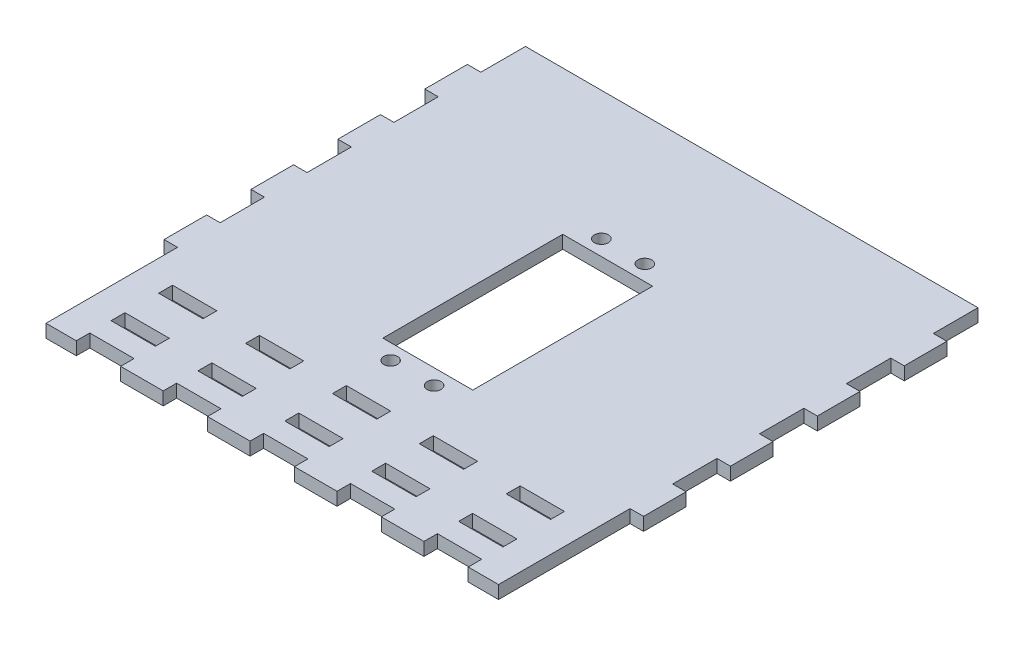
SolidWorks part; units mm, degrees
ref_plane "Front Plane" through (0, 0, 0) normal (0, 0, 1) x (1, 0, 0)
ref_plane "Top Plane" through (0, 0, 0) normal (0, 1, 0) x (1, 0, 0)
ref_plane "Right Plane" through (0, 0, 0) normal (1, 0, 0) x (0, 0, -1)
sketch "Sketch1" plane through (0, 0, 0) normal (0, 1, 0) x (1, 0, 0)
  line L0 (0, 0) -> (0, 21.0585) construction
  line L1 (10.05, -30.75) -> (-10.05, -30.75) construction
  line L2 (-10.05, -30.75) -> (-10.05, 10.05) construction
  line L3 (10.05, 10.05) -> (-10.05, 10.05) construction
  line L4 (10.05, -30.75) -> (10.05, 10.05) construction
  line L5 (10.05, -30.75) -> (-10.05, -30.75) construction
  line L6 (-10.05, -30.75) -> (-10.05, 10.05) construction
  line L7 (10.05, 10.05) -> (-10.05, 10.05) construction
  line L8 (10.05, -30.75) -> (10.05, 10.05) construction
  line L9 (-10.35, -31.05) -> (-10.35, 10.35)
  line L10 (10.35, 10.35) -> (-10.35, 10.35)
  line L11 (10.35, -31.05) -> (10.35, 10.35)
  line L12 (10.35, -31.05) -> (-10.35, -31.05)
  line L13 (-36.8722, 43.5014) -> (-36.8722, -66.843) construction
  line L14 (-55.1722, 43.5014) -> (55.1722, 43.5014)
  line L15 (-55.1722, 43.5014) -> (-55.1722, -66.843)
  line L16 (-55.1722, -66.843) -> (55.1722, -66.843)
  line L17 (55.1722, 43.5014) -> (55.1722, -66.843)
  line L18 (36.8722, 43.5014) -> (36.8722, -66.843) construction
  line L19 (0, 43.5014) -> (0, -66.843) construction
  line L20 (-36.8722, 39.9014) -> (-36.8722, -63.843) construction
  line L21 (0, -11.6708) -> (55.1722, -11.6708) construction
  line L22 (0, -11.6708) -> (55.1722, -66.843) construction
  line L23 (-52.1722, 40.5014) -> (-52.1722, -63.843) construction
  line L24 (52.1722, 40.5014) -> (52.1722, -63.843) construction
  line L25 (-52.1722, 40.5014) -> (52.1722, 40.5014) construction
  line L26 (-52.1722, -63.843) -> (52.1722, -63.843) construction
  line L27 (-52.1722, -63.843) -> (-55.1722, -63.843) construction
  line L28 (-52.1722, -63.843) -> (-52.1722, -66.843) construction
  line L29 (52.1722, 40.5014) -> (52.1722, 43.5014) construction
  line L30 (52.1722, 40.5014) -> (55.1722, 40.5014) construction
  line L31 (-52.1722, -11.6708) -> (-55.1722, -11.6708) construction
  line L32 (56.7, -129.793) -> (59.7, -129.793) construction
  line L33 (-55.1722, -48.543) -> (55.1722, -48.543) construction
  line L34 (-55.1722, -47.793) -> (55.1722, -47.793) construction
  line L35 (55.1722, -47.793) -> (-55.1722, -47.793) construction
  line L36 (55.1722, -44.793) -> (-55.1722, -44.793) construction
  line L37 (-49.1722, -47.793) -> (-49.1722, -44.793) construction
  line L38 (-49.1722, -46.293) -> (-52.1722, -46.293) construction
  line L39 (-55.1722, -58.743) -> (55.1722, -58.743) construction
  line L40 (55.1722, -58.743) -> (-55.1722, -58.743) construction
  line L41 (-55.1722, -55.743) -> (55.1722, -55.743) construction
  line L42 (-49.1722, -55.743) -> (-49.1722, -58.743) construction
  circle A0 centre (0, 0) radius 21.0585 construction
  arc A1 (21.0585, 3.843) -> (-21.0585, 3.843) centre (0, 3.843) ccw construction
  circle A2 centre (-5, -34.6) radius 2 construction
  circle A3 centre (5, -34.6) radius 2 construction
  circle A4 centre (5, 13.9) radius 2 construction
  circle A5 centre (-5, 13.9) radius 2 construction
  circle A6 centre (-5, -34.6) radius 2 construction
  circle A7 centre (5, -34.6) radius 2 construction
  circle A8 centre (5, 13.9) radius 2 construction
  circle A9 centre (-5, 13.9) radius 2 construction
  circle A10 centre (-5, 13.9) radius 1.6
  circle A11 centre (5, 13.9) radius 1.6
  circle A12 centre (5, -34.6) radius 1.6
  circle A13 centre (-5, -34.6) radius 1.6
  dimension "D2" = 3.2
  dimension "D1" = 0.3
extrude "Boss-Extrude1" add sketch "Sketch1" along normal up to vertex (3 mm away)
sketch "Sketch2" plane through (0, 0, 0) normal (0, 1, 0) x (1, 0, 0)
  line L0 (0, -11.6708) -> (55.1722, -11.6708) construction
  line L1 (0, -11.6708) -> (0, 43.5014) construction
  line L2 (0, -11.6708) -> (55.1722, 43.5014) construction
  line L3 (5, 43.5014) -> (5, 40.5014)
  line L4 (15, 40.5014) -> (15, 43.5014)
  line L5 (25, 40.5014) -> (25, 43.5014)
  line L6 (35, 40.5014) -> (35, 43.5014)
  line L7 (45, 40.5014) -> (45, 43.5014)
  line L8 (-55.1722, 43.5014) -> (55.1722, 43.5014) construction
  line L9 (-52.1722, 40.5014) -> (52.1722, 40.5014) construction
  line L10 (52.1722, 33.3292) -> (55.1722, 33.3292)
  line L11 (52.1722, 23.3292) -> (55.1722, 23.3292)
  line L12 (52.1722, 13.3292) -> (55.1722, 13.3292)
  line L13 (52.1722, 3.3292) -> (55.1722, 3.3292)
  line L14 (55.1722, -6.6708) -> (52.1722, -6.6708)
  line L15 (55.1722, -16.6708) -> (52.1722, -16.6708)
  line L16 (52.1722, -26.6708) -> (55.1722, -26.6708)
  line L17 (52.1722, -36.6708) -> (55.1722, -36.6708)
  line L18 (52.1722, -46.6708) -> (55.1722, -46.6708)
  line L19 (52.1722, -56.6708) -> (55.1722, -56.6708)
  line L20 (45, -63.843) -> (45, -66.843)
  line L21 (35, -63.843) -> (35, -66.843)
  line L22 (25, -63.843) -> (25, -66.843)
  line L23 (15, -63.843) -> (15, -66.843)
  line L24 (5, -66.843) -> (5, -63.843)
  line L25 (-5, -66.843) -> (-5, -63.843)
  line L26 (-15, -63.843) -> (-15, -66.843)
  line L27 (-25, -63.843) -> (-25, -66.843)
  line L28 (-35, -63.843) -> (-35, -66.843)
  line L29 (-45, -63.843) -> (-45, -66.843)
  line L30 (-52.1722, -56.6708) -> (-55.1722, -56.6708)
  line L31 (-52.1722, -46.6708) -> (-55.1722, -46.6708)
  line L32 (-52.1722, -36.6708) -> (-55.1722, -36.6708)
  line L33 (-52.1722, -26.6708) -> (-55.1722, -26.6708)
  line L34 (-55.1722, -16.6708) -> (-52.1722, -16.6708)
  line L35 (-55.1722, -6.6708) -> (-52.1722, -6.6708)
  line L36 (-52.1722, 3.3292) -> (-55.1722, 3.3292)
  line L37 (-52.1722, 13.3292) -> (-55.1722, 13.3292)
  line L38 (-52.1722, 23.3292) -> (-55.1722, 23.3292)
  line L39 (-52.1722, 33.3292) -> (-55.1722, 33.3292)
  line L40 (-45, 40.5014) -> (-45, 43.5014)
  line L41 (-35, 40.5014) -> (-35, 43.5014)
  line L42 (-25, 40.5014) -> (-25, 43.5014)
  line L43 (-15, 40.5014) -> (-15, 43.5014)
  line L44 (-5, 43.5014) -> (-5, 40.5014)
  line L45 (55.1722, -44.793) -> (-55.1722, -44.793) construction
  line L48 (-55.1722, -47.793) -> (55.1722, -47.793) construction
  line L49 (55.1722, -44.793) -> (-55.1722, -44.793)
  line L50 (-55.1722, -47.793) -> (55.1722, -47.793)
  line L51 (-15, -47.793) -> (-15, -44.793)
  line L52 (-5, -47.793) -> (-5, -44.793)
  line L53 (5, -47.793) -> (5, -44.793)
  line L54 (15, -47.793) -> (15, -44.793)
  line L55 (25, -47.793) -> (25, -44.793)
  line L56 (35, -47.793) -> (35, -44.793)
  line L57 (45, -47.793) -> (45, -44.793)
  line L58 (-25, -47.793) -> (-25, -44.793)
  line L59 (-35, -47.793) -> (-35, -44.793)
  line L60 (-45, -47.793) -> (-45, -44.793)
  line L61 (52.1722, -63.843) -> (52.1722, -66.843)
  line L62 (52.1722, 40.5014) -> (52.1722, -63.843) construction
  line L63 (55.1722, -63.843) -> (-55.1722, -63.843) construction
  line L64 (-55.1722, -66.843) -> (55.1722, -66.843) construction
  line L65 (-55.1722, -55.743) -> (55.1722, -55.743) construction
  line L66 (-55.1722, -58.743) -> (55.1722, -58.743) construction
  line L67 (-55.1722, -55.743) -> (55.1722, -55.743)
  line L68 (-55.1722, -58.743) -> (55.1722, -58.743)
  line L69 (-45, -55.743) -> (-45, -58.743)
  line L70 (-15, -55.743) -> (-15, -58.743)
  line L71 (-35, -55.743) -> (-35, -58.743)
  line L72 (-25, -55.743) -> (-25, -58.743)
  line L73 (-5, -58.743) -> (-5, -55.743)
  line L74 (5, -58.743) -> (5, -55.743)
  line L75 (15, -58.743) -> (15, -55.743)
  line L76 (25, -58.743) -> (25, -55.743)
  line L77 (45, -55.743) -> (45, -58.743)
  line L78 (35, -58.743) -> (35, -55.743)
sketch "Sketch3" plane through (0, 0, 0) normal (0, 1, 0) x (1, 0, 0)
  line L0 (0, -11.6708) -> (55.1722, 43.5014) construction
  line L1 (0, -11.6708) -> (55.1722, -11.6708) construction
  line L2 (0, -11.6708) -> (0, 43.5014) construction
  line L3 (52.1722, -6.6708) -> (52.0722, -6.6708) construction
  line L4 (52.0722, 3.4292) -> (55.2722, 3.4292)
  line L5 (52.0722, 3.4292) -> (52.0722, -6.7708)
  line L6 (52.0722, -6.7708) -> (55.2722, -6.7708)
  line L7 (55.2722, 3.4292) -> (55.2722, -6.7708)
  line L8 (52.0722, 13.2292) -> (55.2722, 13.2292)
  line L9 (52.0722, 13.2292) -> (52.0722, 23.4292)
  line L10 (52.0722, 23.4292) -> (55.2722, 23.4292)
  line L11 (55.2722, 13.2292) -> (55.2722, 23.4292)
  line L12 (52.0722, 33.2292) -> (55.2722, 33.2292)
  line L13 (52.0722, 33.2292) -> (52.0722, 43.6014)
  line L14 (52.0722, 43.6014) -> (55.2722, 43.6014)
  line L15 (55.2722, 33.2292) -> (55.2722, 43.6014)
  line L16 (52.1722, -6.6708) -> (52.1722, -6.7708) construction
  line L17 (55.1722, 3.3292) -> (55.2722, 3.3292) construction
  line L18 (55.1722, 3.3292) -> (55.1722, 3.4292) construction
  line L19 (52.1722, 13.3292) -> (52.1722, 13.2292) construction
  line L20 (52.1722, 23.3292) -> (52.1722, 23.4292) construction
  line L21 (52.1722, 33.3292) -> (52.1722, 33.2292) construction
  line L22 (52.1722, 43.5014) -> (52.1722, 43.6014) construction
  line L23 (45, -44.793) -> (45, -44.693) construction
  line L24 (45.1, -47.893) -> (34.9, -47.893)
  line L25 (45.1, -47.893) -> (45.1, -44.693)
  line L26 (45.1, -44.693) -> (34.9, -44.693)
  line L27 (52.0722, -26.7708) -> (55.2722, -26.7708)
  line L28 (52.0722, -26.7708) -> (52.0722, -16.5708)
  line L29 (52.0722, -16.5708) -> (55.2722, -16.5708)
  line L30 (55.2722, -26.7708) -> (55.2722, -16.5708)
  line L31 (34.9, -47.893) -> (34.9, -44.693)
  line L32 (25.1, -47.893) -> (14.9, -47.893)
  line L33 (25.1, -47.893) -> (25.1, -44.693)
  line L34 (25.1, -44.693) -> (14.9, -44.693)
  line L35 (14.9, -47.893) -> (14.9, -44.693)
  line L36 (5.1, -47.893) -> (-5.1, -47.893)
  line L37 (5.1, -47.893) -> (5.1, -44.693)
  line L38 (5.1, -44.693) -> (-5.1, -44.693)
  line L39 (-5.1, -47.893) -> (-5.1, -44.693)
  line L40 (45, -47.793) -> (45, -47.893) construction
  line L41 (45, -44.793) -> (45.1, -44.793) construction
  line L42 (35, -44.793) -> (34.9, -44.793) construction
  line L43 (25, -44.793) -> (25.1, -44.793) construction
  line L44 (15, -44.793) -> (14.9, -44.793) construction
  line L45 (5, -44.793) -> (5.1, -44.793) construction
  line L46 (-25.1, -47.893) -> (-14.9, -47.893)
  line L47 (-14.9, -47.893) -> (-14.9, -44.693)
  line L48 (-25.1, -44.693) -> (-14.9, -44.693)
  line L49 (-25.1, -47.893) -> (-25.1, -44.693)
  line L50 (-45.1, -47.893) -> (-34.9, -47.893)
  line L51 (-45.1, -47.893) -> (-45.1, -44.693)
  line L52 (-45.1, -44.693) -> (-34.9, -44.693)
  line L53 (-34.9, -47.893) -> (-34.9, -44.693)
  line L54 (-52.0722, 33.2292) -> (-55.2722, 33.2292)
  line L55 (-55.2722, 33.2292) -> (-55.2722, 43.6014)
  line L56 (-52.0722, 43.6014) -> (-55.2722, 43.6014)
  line L57 (-52.0722, 33.2292) -> (-52.0722, 43.6014)
  line L58 (-52.0722, 13.2292) -> (-55.2722, 13.2292)
  line L59 (-55.2722, 13.2292) -> (-55.2722, 23.4292)
  line L60 (-52.0722, 23.4292) -> (-55.2722, 23.4292)
  line L61 (-52.0722, 13.2292) -> (-52.0722, 23.4292)
  line L62 (-52.0722, 3.4292) -> (-55.2722, 3.4292)
  line L63 (-55.2722, 3.4292) -> (-55.2722, -6.7708)
  line L64 (-52.0722, -6.7708) -> (-55.2722, -6.7708)
  line L65 (-52.0722, 3.4292) -> (-52.0722, -6.7708)
  line L66 (-52.0722, -26.7708) -> (-55.2722, -26.7708)
  line L67 (-52.0722, -26.7708) -> (-52.0722, -16.5708)
  line L68 (-52.0722, -16.5708) -> (-55.2722, -16.5708)
  line L69 (-55.2722, -26.7708) -> (-55.2722, -16.5708)
  line L70 (45, -55.743) -> (45, -55.643) construction
  line L71 (34.9, -66.943) -> (45.1, -66.943)
  line L72 (34.9, -66.943) -> (34.9, -63.743)
  line L73 (34.9, -63.743) -> (45.1, -63.743)
  line L74 (45.1, -66.943) -> (45.1, -63.743)
  line L75 (52.0722, -66.943) -> (55.2722, -66.943)
  line L76 (52.0722, -66.943) -> (52.0722, -36.5708)
  line L77 (34.9, -58.843) -> (45.1, -58.843)
  line L78 (55.2722, -66.943) -> (55.2722, -36.5708)
  line L79 (34.9, -58.843) -> (34.9, -55.643)
  line L80 (34.9, -55.643) -> (45.1, -55.643)
  line L81 (52.0722, -36.5708) -> (55.2722, -36.5708)
  line L82 (45.1, -58.843) -> (45.1, -55.643)
  line L83 (14.9, -66.943) -> (25.1, -66.943)
  line L84 (14.9, -66.943) -> (14.9, -63.743)
  line L85 (14.9, -63.743) -> (25.1, -63.743)
  line L86 (25.1, -66.943) -> (25.1, -63.743)
  line L87 (5.1, -66.943) -> (-5.1, -66.943)
  line L88 (5.1, -66.943) -> (5.1, -63.743)
  line L89 (5.1, -63.743) -> (-5.1, -63.743)
  line L90 (-5.1, -66.943) -> (-5.1, -63.743)
  line L91 (25.1, -58.843) -> (14.9, -58.843)
  line L92 (25.1, -58.843) -> (25.1, -55.643)
  line L93 (25.1, -55.643) -> (14.9, -55.643)
  line L94 (14.9, -58.843) -> (14.9, -55.643)
  line L95 (-5.1, -55.643) -> (5.1, -55.643)
  line L96 (-5.1, -55.643) -> (-5.1, -58.843)
  line L97 (-5.1, -58.843) -> (5.1, -58.843)
  line L98 (5.1, -55.643) -> (5.1, -58.843)
  line L99 (45, -58.743) -> (45, -58.843) construction
  line L100 (45, -63.843) -> (45, -63.743) construction
  line L101 (45, -66.843) -> (45, -66.943) construction
  line L102 (52.1722, -36.6708) -> (52.1722, -36.5708) construction
  line L103 (-34.9, -66.943) -> (-34.9, -63.743)
  line L104 (-34.9, -66.943) -> (-45.1, -66.943)
  line L105 (-45.1, -66.943) -> (-45.1, -63.743)
  line L106 (-34.9, -63.743) -> (-45.1, -63.743)
  line L107 (-34.9, -58.843) -> (-34.9, -55.643)
  line L108 (-34.9, -58.843) -> (-45.1, -58.843)
  line L109 (-45.1, -58.843) -> (-45.1, -55.643)
  line L110 (-34.9, -55.643) -> (-45.1, -55.643)
  line L111 (-25.1, -58.843) -> (-25.1, -55.643)
  line L112 (-25.1, -58.843) -> (-14.9, -58.843)
  line L113 (-14.9, -58.843) -> (-14.9, -55.643)
  line L114 (-25.1, -55.643) -> (-14.9, -55.643)
  line L115 (-14.9, -66.943) -> (-14.9, -63.743)
  line L116 (-14.9, -66.943) -> (-25.1, -66.943)
  line L117 (-25.1, -66.943) -> (-25.1, -63.743)
  line L118 (-14.9, -63.743) -> (-25.1, -63.743)
  line L119 (-52.0722, -66.943) -> (-55.2722, -66.943)
  line L120 (-55.2722, -66.943) -> (-55.2722, -36.5708)
  line L121 (-52.0722, -36.5708) -> (-55.2722, -36.5708)
  line L122 (-52.0722, -66.943) -> (-52.0722, -36.5708)
extrude "Cut-Extrude1" cut sketch "Sketch3" along normal through all
